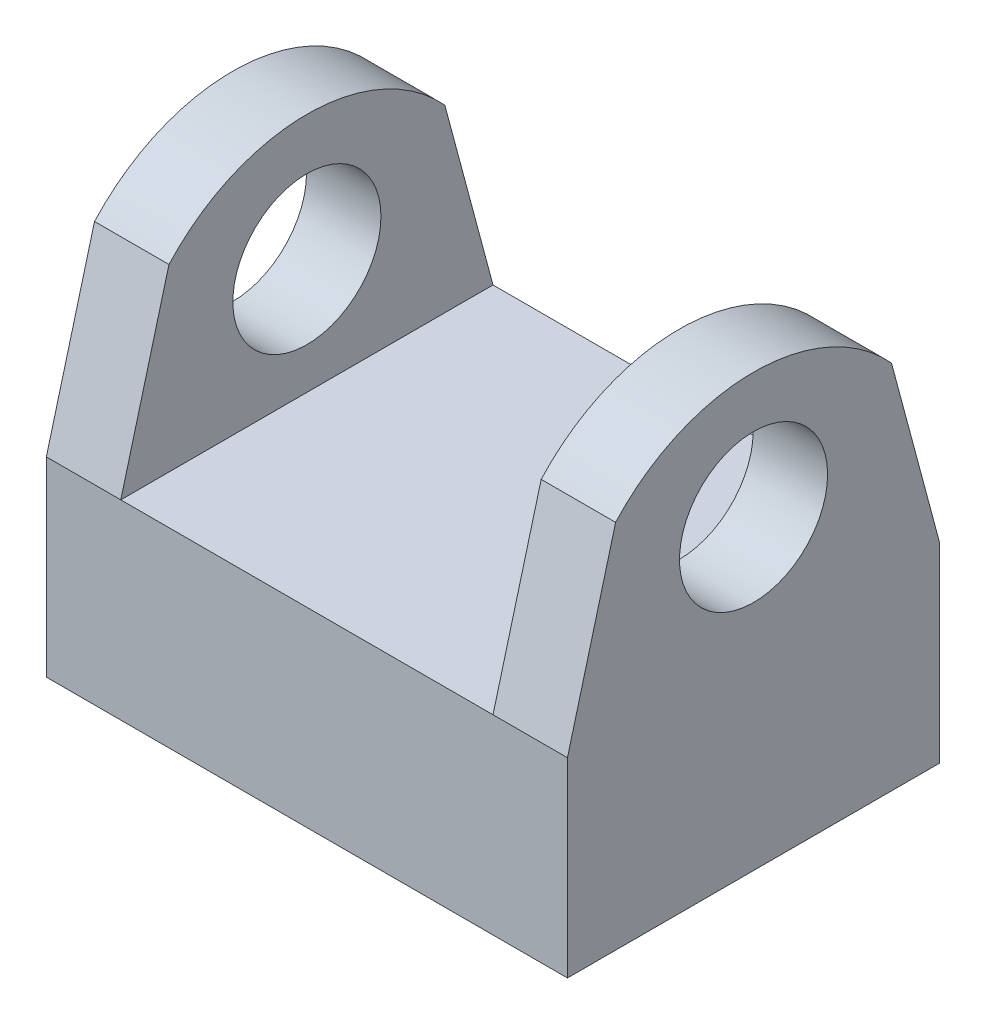
SolidWorks part; units mm, degrees
material "ABS"
ref_plane "Front Plane" through (0, 0, 0) normal (0, 0, 1) x (1, 0, 0)
ref_plane "Top Plane" through (0, 0, 0) normal (0, 1, 0) x (1, 0, 0)
ref_plane "Right Plane" through (0, 0, 0) normal (1, 0, 0) x (0, 0, -1)
sketch "Sketch1" plane through (0, 0, 0) normal (0, 1, 0) x (1, 0, 0)
  line L1 (-17.78, -12.7) -> (17.78, -12.7)
  line L2 (-17.78, -12.7) -> (-17.78, 12.7)
  line L3 (-17.78, 12.7) -> (17.78, 12.7)
  line L4 (17.78, -12.7) -> (17.78, 12.7)
  line L5 (-17.78, -12.7) -> (17.78, 12.7) construction
  line L6 (-17.78, 12.7) -> (17.78, -12.7) construction
  point P0 (0, 0)
  dimension "D1" = 35.56
extrude "Boss-Extrude1" add sketch "Sketch1" along normal blind 13.0175 contours L3 L4 L1 L2
sketch "Sketch2" plane through (17.78, 0, 0) normal (1, 0, 0) x (0, 0, -1)
  line L0 (-12.7, 13.0175) -> (-9.413, 25.2848)
  line L1 (12.7, 13.0175) -> (9.413, 25.2848)
  line L2 (-12.7, 13.0175) -> (12.7, 13.0175) construction
  line L3 (-12.7, 13.0175) -> (12.7, 13.0175)
  arc A1 (-9.413, 25.2848) -> (9.413, 25.2848) centre (0, 16.7437) cw
  dimension "D1" = 75
  dimension "D2" = 75
extrude "Boss-Extrude2" add sketch "Sketch2" against normal blind 5.08
ref_plane "Plane1" through (0, 0, 0) normal (1, 0, 0) x (0, 0, -1)
mirror "Mirror1" about plane through (0, 0, 0) normal (1, 0, 0) of "Boss-Extrude2"
sketch "Sketch3" plane through (17.78, 0, 0) normal (1, 0, 0) x (0, 0, -1)
  line L0 (-12.7, 0) -> (12.7, 0) construction
  circle A0 centre (0, 20.8915) radius 5.0532
  dimension "D1" = 20.8915
extrude "Cut-Extrude1" cut sketch "Sketch3" against normal through all
